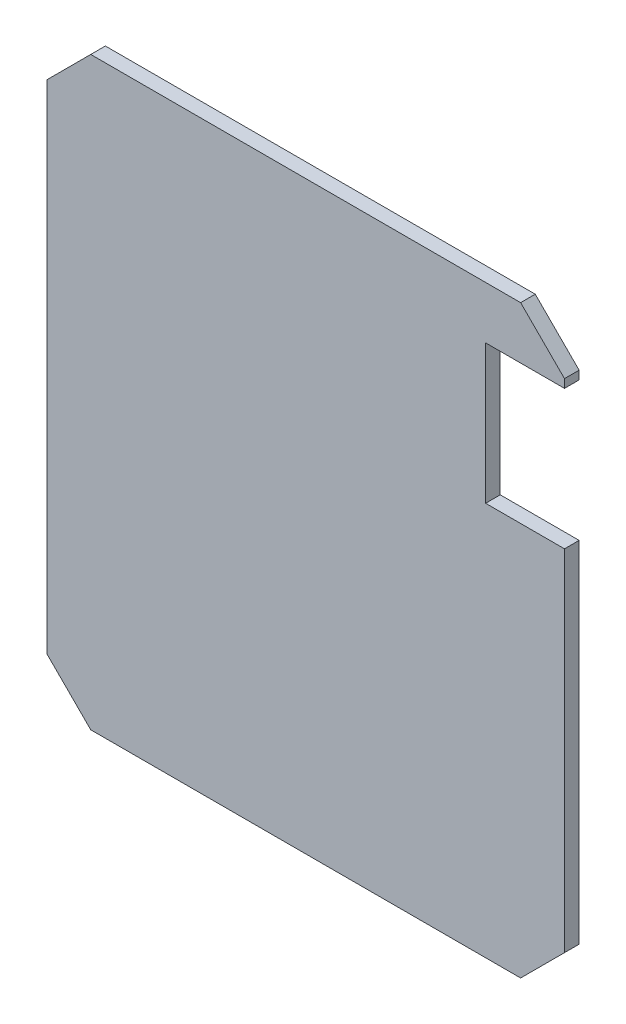
SolidWorks part; units mm, degrees
ref_plane "前视基准面" through (0, 0, 0) normal (0, 0, 1) x (1, 0, 0)
ref_plane "上视基准面" through (0, 0, 0) normal (0, 1, 0) x (1, 0, 0)
ref_plane "右视基准面" through (0, 0, 0) normal (1, 0, 0) x (0, 0, -1)
sketch "草图1" plane through (0, 0, 0) normal (0, 0, 1) x (1, 0, 0)
  line L0 (-17.75, 17) -> (-17.75, -17) construction
  line L1 (14.7, -20) -> (-14.7, -20)
  line L2 (17.7, -17) -> (17.7, 17)
  line L3 (14.7, 20) -> (-14.7, 20)
  line L4 (-17.7, -17) -> (-17.7, 17)
  line L5 (17.7, -20) -> (-17.7, 20) construction
  line L6 (17.7, 20) -> (-17.7, -20) construction
  line L7 (-14.7, 20) -> (-17.7, 17)
  line L8 (-14.7, -20) -> (-17.7, -17)
  line L9 (17.7, -17) -> (14.7, -20)
  line L10 (17.7, 17) -> (14.7, 20)
  point P0 (0, 0)
  dimension "D1" = 0.05
  dimension "D2" = 40
extrude "凸台-拉伸1" add sketch "草图1" along normal blind 1
sketch "草图2" plane through (0, 0, 1) normal (0, 0, 1) x (1, 0, 0)
  line L0 (17.7, -17) -> (17.7, 17) construction
  line L1 (17.7, 16.4206) -> (12.3058, 16.4206)
  line L2 (17.7, 16.4206) -> (17.7, 6.9197)
  line L3 (17.7, 6.9197) -> (12.3058, 6.9197)
  line L4 (12.3058, 16.4206) -> (12.3058, 6.9197)
  line L5 (14.3059, 15.4206) -> (15.5211, 15.4206) construction
  line L6 (14.3059, 7.9197) -> (15.5211, 7.9197) construction
  line L7 (13.3058, 8.4697) -> (13.3058, 7.9197) construction
  dimension "D1" = 1
  dimension "D2" = 1
  dimension "D3" = 1
extrude "切除-拉伸1" cut sketch "草图2" against normal through all
